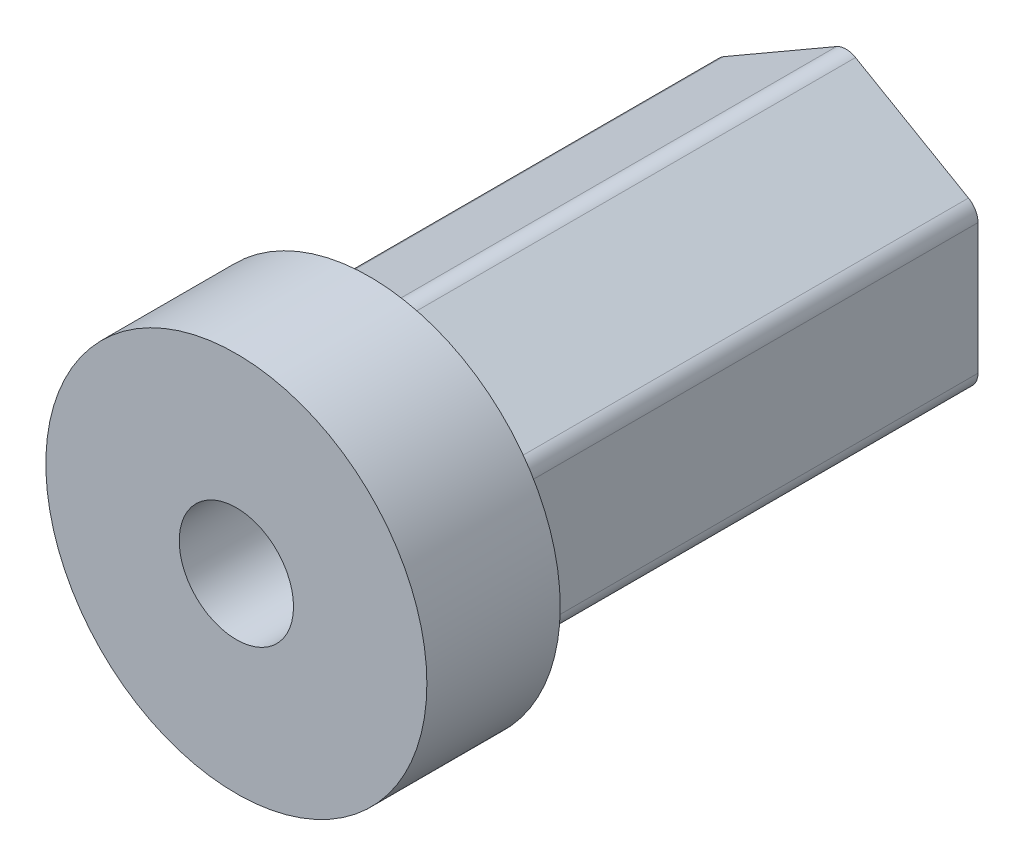
SolidWorks part; units mm, degrees
material "2014 Alloy"
ref_plane "Front Plane" through (0, 0, 0) normal (0, 0, 1) x (1, 0, 0)
ref_plane "Top Plane" through (0, 0, 0) normal (0, 1, 0) x (1, 0, 0)
ref_plane "Right Plane" through (0, 0, 0) normal (1, 0, 0) x (0, 0, -1)
sketch "Sketch2" plane through (0, 0, 0) normal (1, 0, 0) x (0, 0, -1)
  line L0 (0, 0) -> (38.379, 0) construction
  line L1 (-7, 3) -> (25, 3)
  line L2 (25, 3) -> (25, 8)
  line L3 (25, 8) -> (0, 8)
  line L4 (0, 8) -> (0, 10)
  line L5 (0, 10) -> (-7, 10)
  line L6 (-7, 10) -> (-7, 3)
  dimension "D1" = 6
  dimension "D2" = 5
  dimension "D3" = 7
  dimension "D4" = 25
  dimension "D5" = 7
  dimension "D6" = 25
revolve "Revolve1" add sketch "Sketch2" angle 360 about L0
sketch "Sketch3" plane through (0, 0, -25) normal (0, 0, -1) x (-1, 0, 0)
  line L1 (0, -8) -> (6.9282, -4)
  line L2 (6.9282, -4) -> (6.9282, 4)
  line L3 (6.9282, 4) -> (0, 8)
  line L4 (0, 8) -> (-6.9282, 4)
  line L5 (-6.9282, 4) -> (-6.9282, -4)
  line L6 (-6.9282, -4) -> (0, -8)
  circle A0 centre (0, 0) radius 6.9282 construction
  circle A1 centre (0, 0) radius 8
  circle A2 centre (0, 0) radius 8 construction
  circle M1 centre (0, 0) radius 8
extrude "Cut-Extrude1" cut sketch "Sketch3" against normal blind 25 contours L4 M1 | L5 M1 | L6 M1 | L1 M1 | L2 M1 | L3 M1
fillet "Fillet1" radius 1 6 edges at (-6.9282, 4, -12.5) (-6.9282, -4, -12.5) (0, -8, -12.5) (6.9282, -4, -12.5) (6.9282, 4, -12.5) (0, 8, -12.5)
